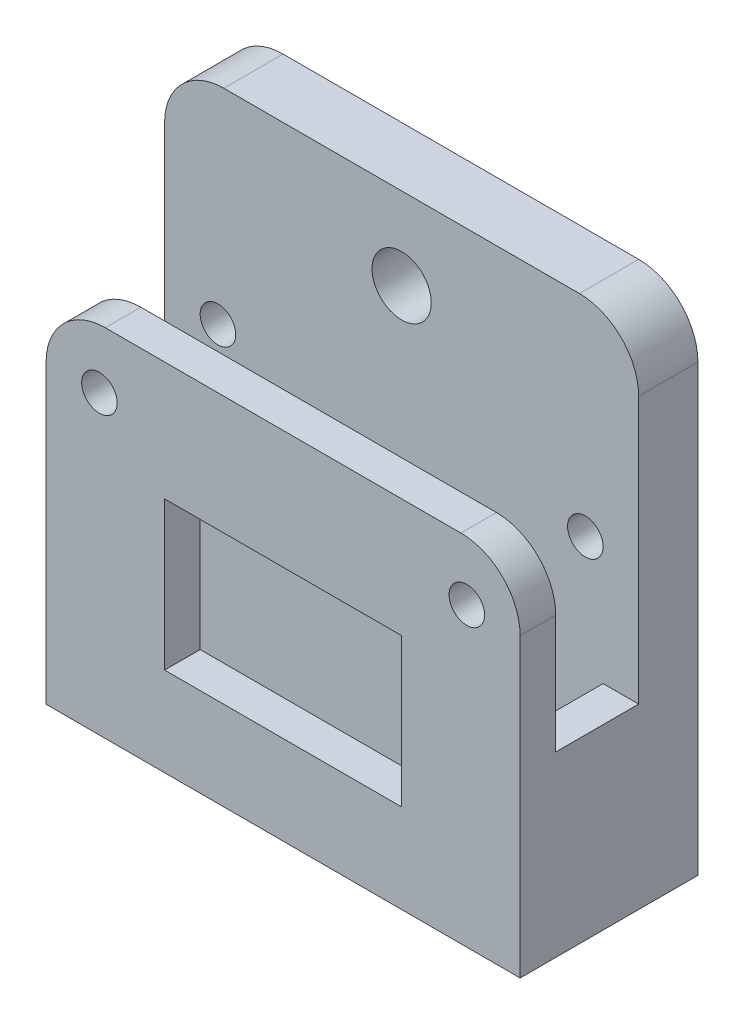
SolidWorks part; units mm, degrees
ref_plane "Front Plane" through (0, 0, 0) normal (0, 0, 1) x (1, 0, 0)
ref_plane "Top Plane" through (0, 0, 0) normal (0, 1, 0) x (1, 0, 0)
ref_plane "Right Plane" through (0, 0, 0) normal (1, 0, 0) x (0, 0, -1)
sketch "Sketch1" plane through (0, 0, 0) normal (0, 0, 1) x (1, 0, 0)
  line L9 (380.4587, 354.0913) -> (420.4587, 354.0913)
  line L10 (380.4587, 354.0913) -> (380.4587, 304.0913)
  line L11 (380.4587, 304.0913) -> (420.4587, 304.0913)
  line L12 (420.4587, 354.0913) -> (420.4587, 304.0913)
  dimension "D1" = 50
  dimension "D2" = 40
extrude "Boss-Extrude2" add sketch "Sketch1" along normal blind 15
sketch "Sketch2" plane through (0, 354.0913, 0) normal (0, 1, 0) x (1, 0, 0)
  line L0 (380.4587, -15) -> (380.4587, 0) construction
  line L1 (383.4587, -5) -> (417.4587, -5)
  line L2 (383.4587, -5) -> (383.4587, -12)
  line L3 (383.4587, -12) -> (417.4587, -12)
  line L4 (417.4587, -5) -> (417.4587, -12)
  line L5 (420.4587, -15) -> (420.4587, 0) construction
  line L6 (-55, 0) -> (55, 0) construction
  line L7 (420.4587, -15) -> (380.4587, -15) construction
  dimension "D1" = 3
  dimension "D2" = 3
  dimension "D3" = 5
  dimension "D4" = 3
extrude "Cut-Extrude1" cut sketch "Sketch2" against normal blind 50 contours L2 L1 L4 L3
sketch "Sketch3" plane through (380.4587, 0, 0) normal (-1, 0, 0) x (0, 0, 1)
  line L0 (15, 304.0913) -> (0, 304.0913) construction
  line L1 (5, 324.0913) -> (12, 324.0913)
  line L2 (5, 324.0913) -> (5, 354.0913)
  line L3 (5, 354.0913) -> (12, 354.0913)
  line L4 (12, 324.0913) -> (12, 354.0913)
  line L5 (0, -55) -> (0, 55) construction
  line L6 (15, 354.0913) -> (15, 304.0913) construction
  dimension "D1" = 20
  dimension "D2" = 5
  dimension "D3" = 3
  dimension "D4" = 30
extrude "Cut-Extrude2" cut sketch "Sketch3" against normal blind 50
sketch "Sketch5" plane through (380.4587, 0, 0) normal (-1, 0, 0) x (0, 0, 1)
sketch "Sketch6" plane through (0, 0, 0) normal (0, 0, -1) x (-1, 0, 0)
  line L0 (-420.4587, 304.0913) -> (-420.4587, 354.0913) construction
  line L1 (-380.4587, 354.0913) -> (-420.4587, 354.0913)
  line L2 (-380.4587, 354.0913) -> (-380.4587, 351.5913)
  line L3 (-380.4587, 351.5913) -> (-420.4587, 351.5913)
  line L4 (-420.4587, 354.0913) -> (-420.4587, 351.5913)
  line L5 (-380.4587, 354.0913) -> (-380.4587, 304.0913) construction
  line L6 (-420.4587, 304.0913) -> (-380.4587, 304.0913)
  line L7 (-420.4587, 304.0913) -> (-420.4587, 309.0766)
  line L8 (-420.4587, 309.0766) -> (-380.4587, 309.0766)
  line L9 (-380.4587, 304.0913) -> (-380.4587, 309.0766)
  dimension "D1" = 2.5
extrude "Cut-Extrude4" cut sketch "Sketch6" against normal blind 50
sketch "Sketch7" plane through (0, 0, 15) normal (0, 0, 1) x (1, 0, 0)
  line L0 (420.4587, 309.0766) -> (420.4587, 351.5913) construction
  line L1 (380.4587, 351.5913) -> (420.4587, 351.5913)
  line L2 (380.4587, 351.5913) -> (380.4587, 339.0913)
  line L3 (380.4587, 339.0913) -> (420.4587, 339.0913)
  line L4 (420.4587, 351.5913) -> (420.4587, 339.0913)
  dimension "D1" = 12.5
extrude "Cut-Extrude5" cut sketch "Sketch7" against normal blind 5
sketch "Sketch8" plane through (0, 0, 15) normal (0, 0, 1) x (1, 0, 0)
  line L1 (390.4587, 316.5766) -> (410.4587, 316.5766)
  line L2 (390.4587, 316.5766) -> (390.4587, 329.0913)
  line L3 (390.4587, 329.0913) -> (410.4587, 329.0913)
  line L4 (410.4587, 316.5766) -> (410.4587, 329.0913)
  line L6 (420.4587, 309.0766) -> (380.4587, 309.0766) construction
  line L7 (380.4587, 339.0913) -> (420.4587, 339.0913) construction
  line L8 (380.4587, 339.0913) -> (380.4587, 309.0766) construction
  line L9 (420.4587, 309.0766) -> (420.4587, 339.0913) construction
  point P8 (390.4587, 322.8339)
  dimension "D1" = 7.5
  dimension "D2" = 10
  dimension "D3" = 10
  dimension "D4" = 10
extrude "Cut-Extrude7" cut sketch "Sketch8" against normal blind 5
sketch "Sketch11" plane through (0, 0, 5) normal (0, 0, 1) x (1, 0, 0)
  line L0 (380.4587, 351.5913) -> (380.4587, 324.0913) construction
  line L2 (380.4587, 351.5913) -> (380.4587, 309.0766) construction
  circle A0 centre (400.4587, 344.6606) radius 2.5
  circle A1 centre (400.4587, 322.933) radius 2.5
  dimension "D1" = 20
  dimension "D3" = 5
  dimension "D2" = 20
extrude "Cut-Extrude10" cut sketch "Sketch11" against normal blind 5
sketch "Sketch12" plane through (0, 0, 15) normal (0, 0, 1) x (1, 0, 0)
  line L2 (380.4587, 324.0913) -> (380.4587, 354.0913) construction
  line L3 (420.4587, 309.0766) -> (420.4587, 339.0913) construction
  line L4 (380.4587, 339.0913) -> (420.4587, 339.0913) construction
  circle A3 centre (415.9587, 334.0913) radius 1.5
  circle A4 centre (384.9587, 334.0913) radius 1.5
  dimension "D1" = 4.5
  dimension "D3" = 5
  dimension "D2" = 4.5
extrude "Cut-Extrude11" cut sketch "Sketch12" against normal blind 15
fillet "Fillet2" radius 5 1 edges at (380.4587, 339.0913, 13.5)
fillet "Fillet3" radius 5 3 edges at (380.4587, 351.5913, 2.5) (420.4587, 351.5913, 2.5) (420.4587, 339.0913, 13.5)
